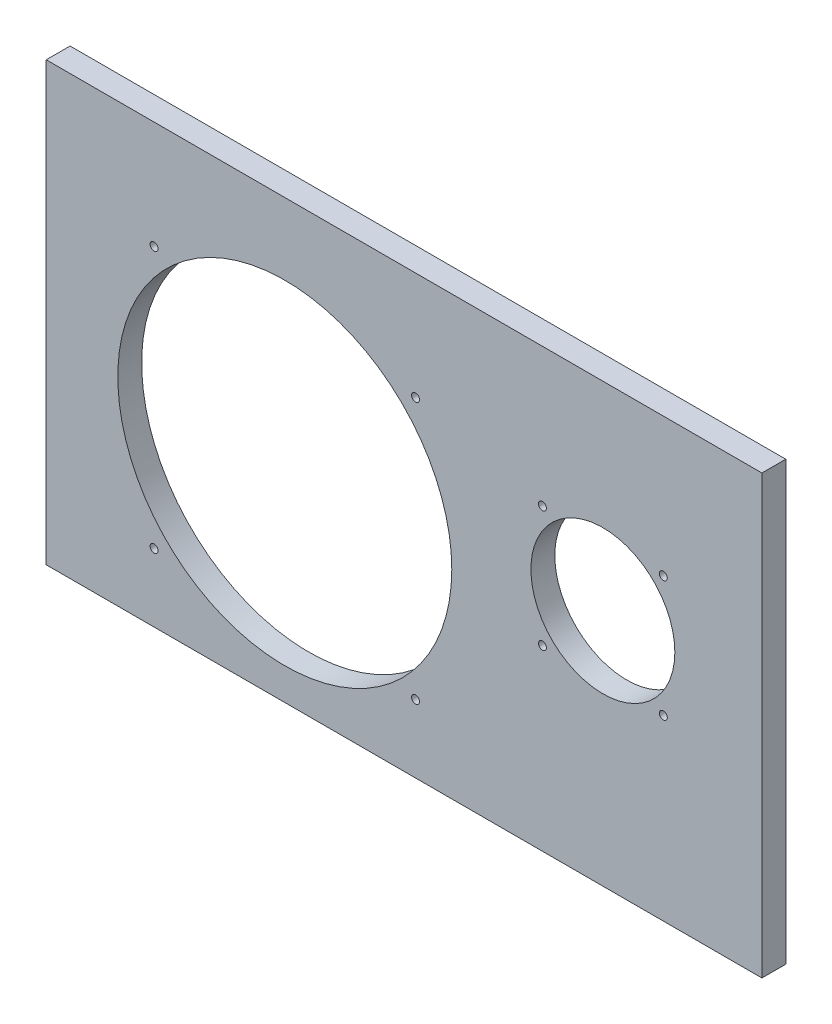
SolidWorks part; units mm, degrees
ref_plane "Front Plane" through (0, 0, 0) normal (0, 0, 1) x (1, 0, 0)
ref_plane "Top Plane" through (0, 0, 0) normal (0, 1, 0) x (1, 0, 0)
ref_plane "Right Plane" through (0, 0, 0) normal (1, 0, 0) x (0, 0, -1)
sketch "Sketch1" plane through (0, 0, 0) normal (0, 0, 1) x (1, 0, 0)
  line L1 (0, 0) -> (180, 0)
  line L2 (0, 0) -> (0, 110)
  line L3 (0, 110) -> (180, 110)
  line L4 (180, 0) -> (180, 110)
  circle A0 centre (60, 50) radius 42
  circle A1 centre (140, 60) radius 18.1
extrude "Boss-Extrude1" add sketch "Sketch1" along normal blind 6
sketch "Sketch2" plane through (0, 0, 0) normal (0, 0, 1) x (1, 0, 0)
  point P0 (60, 50)
sketch "Sketch3" plane through (0, 0, 0) normal (0, 0, 1) x (1, 0, 0)
  line L0 (60, 50) -> (92.8805, 82.8805) construction
  line L1 (60, 50) -> (27.1195, 82.8805) construction
  line L2 (60, 50) -> (27.1195, 17.1195) construction
  line L3 (60, 50) -> (92.8805, 17.1195) construction
  line L4 (140, 60) -> (155.2028, 75.2028) construction
  line L5 (155.2028, 75.2028) -> (140, 60) construction
  line L6 (124.7972, 75.2028) -> (140, 60) construction
  line L7 (140, 60) -> (124.7972, 44.7972) construction
  line L8 (124.7972, 44.7972) -> (140, 60) construction
  line L9 (155.2028, 44.7972) -> (140, 60) construction
  line L10 (140, 60) -> (139.5199, 60.5643)
  circle A0 centre (92.8805, 82.8805) radius 1
  circle A1 centre (27.1195, 82.8805) radius 1
  circle A2 centre (27.1195, 17.1195) radius 1
  circle A3 centre (92.8805, 17.1195) radius 1
  circle A4 centre (155.2028, 75.2028) radius 1
  circle A5 centre (124.7972, 75.2028) radius 1
  circle A6 centre (124.7972, 44.7972) radius 1
  circle A7 centre (155.2028, 44.7972) radius 1
extrude "Cut-Extrude1" cut sketch "Sketch3" along normal blind 30 contours A1 | A0 | A2 | A3 | A6 | A5 | A4 | A7
